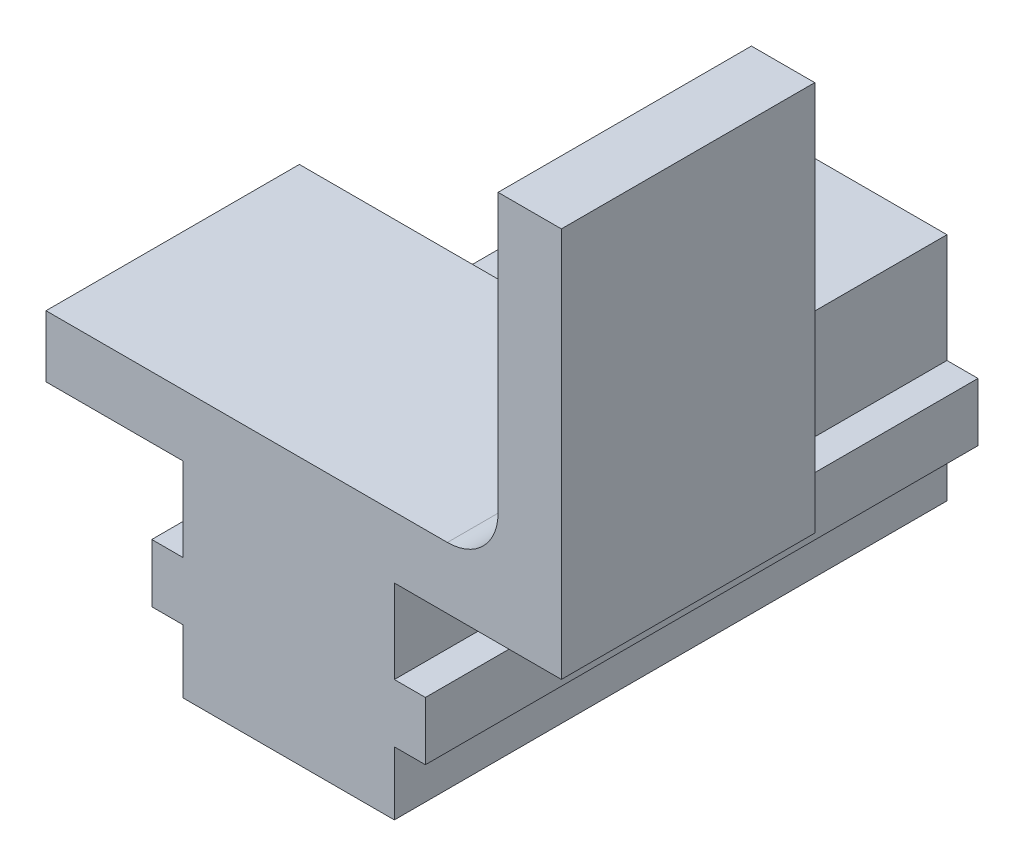
SolidWorks part; units mm, degrees
ref_plane "Front Plane" through (0, 0, 0) normal (0, 0, 1) x (1, 0, 0)
ref_plane "Top Plane" through (0, 0, 0) normal (0, 1, 0) x (1, 0, 0)
ref_plane "Right Plane" through (0, 0, 0) normal (1, 0, 0) x (0, 0, -1)
sketch "Sketch1" plane through (0, 0, 0) normal (0, 0, 1) x (1, 0, 0)
  line L0 (0, 0) -> (0, -4.191)
  line L1 (0, -4.191) -> (-1.5558, -4.191)
  line L2 (-1.5558, -4.191) -> (-1.5558, -7.112)
  line L3 (-1.5558, -7.112) -> (0, -7.112)
  line L4 (0, -7.112) -> (0, -10.287)
  line L5 (0, -10.287) -> (10.6045, -10.287)
  line L6 (10.6045, -10.287) -> (10.6045, -7.112)
  line L7 (10.6045, -7.112) -> (12.1603, -7.112)
  line L8 (12.1603, -7.112) -> (12.1603, -4.191)
  line L9 (12.1603, -4.191) -> (10.6045, -4.191)
  line L10 (10.6045, -4.191) -> (10.6045, 0)
  line L11 (10.6045, 0) -> (18.9772, 0)
  line L12 (18.9772, 0) -> (18.9772, 19.558)
  line L13 (18.9772, 19.558) -> (15.8022, 19.558)
  line L14 (15.8022, 19.558) -> (15.8022, 3.089)
  line L15 (15.8022, 3.089) -> (-6.858, 3.089)
  line L16 (-6.858, 3.089) -> (-6.858, 0)
  line L17 (-6.858, 0) -> (0, 0)
  line L18 (5.3022, -10.287) -> (5.3022, 13.589) construction
  circle A0 centre (5.3022, 13.589) radius 10.5 construction
  dimension "D9" = 21
  dimension "D1" = 10.6045
  dimension "D2" = 2.921
  dimension "D3" = 3.175
  dimension "D4" = 4.191
  dimension "D5" = 13.716
  dimension "D6" = 3.175
  dimension "D7" = 19.558
  dimension "D8" = 23.876
  dimension "D10" = 6.858
extrude "Boss-Extrude1" add sketch "Sketch1" along normal blind 12.7
fillet "Fillet1" radius 2.54 1 edges at (15.8022, 3.089, 6.35)
sketch "Sketch2" plane through (0, 0, 0) normal (0, 0, 1) x (1, 0, 0)
  line L0 (0, 0) -> (0, 1.27)
  line L1 (0, 1.27) -> (10.6045, 1.27)
  line L2 (10.6045, 1.27) -> (10.6045, 0)
  line L18 (-6.858, 0) -> (0, 0)
  line L19 (0, 0) -> (0, -4.191)
  line L20 (0, -4.191) -> (-1.5558, -4.191)
  line L21 (-1.5558, -4.191) -> (-1.5558, -7.112)
  line L22 (-1.5558, -7.112) -> (0, -7.112)
  line L23 (0, -7.112) -> (0, -10.287)
  line L24 (0, -10.287) -> (10.6045, -10.287)
  line L25 (10.6045, -10.287) -> (10.6045, -7.112)
  line L26 (10.6045, -7.112) -> (12.1603, -7.112)
  line L27 (12.1603, -7.112) -> (12.1603, -4.191)
  line L28 (12.1603, -4.191) -> (10.6045, -4.191)
  line L29 (10.6045, -4.191) -> (10.6045, 0)
  line L30 (10.6045, 0) -> (18.9772, 0)
  line L31 (18.9772, 0) -> (18.9772, 19.558)
  line L32 (18.9772, 19.558) -> (15.8022, 19.558)
  line L33 (15.8022, 19.558) -> (15.8022, 5.629)
  line L34 (13.2622, 3.089) -> (-6.858, 3.089)
  line L35 (-6.858, 3.089) -> (-6.858, 0)
  line L37 (0, 0) -> (0, -4.191)
  line L38 (0, -4.191) -> (-1.5558, -4.191)
  line L39 (-1.5558, -4.191) -> (-1.5558, -7.112)
  line L40 (-1.5558, -7.112) -> (0, -7.112)
  line L41 (0, -7.112) -> (0, -10.287)
  line L42 (0, -10.287) -> (10.6045, -10.287)
  line L43 (10.6045, -10.287) -> (10.6045, -7.112)
  line L44 (10.6045, -7.112) -> (12.1603, -7.112)
  line L45 (12.1603, -7.112) -> (12.1603, -4.191)
  line L46 (12.1603, -4.191) -> (10.6045, -4.191)
  line L47 (10.6045, -4.191) -> (10.6045, 0)
  arc A1 (13.2622, 3.089) -> (15.8022, 5.629) centre (13.2622, 5.629) ccw
  dimension "D2" = 1.27
  dimension "D1" = 0
extrude "Boss-Extrude2" add sketch "Sketch2" against normal blind 15
fillet "Fillet2" radius 1.27 1 edges at (5.3022, 1.27, 0)
